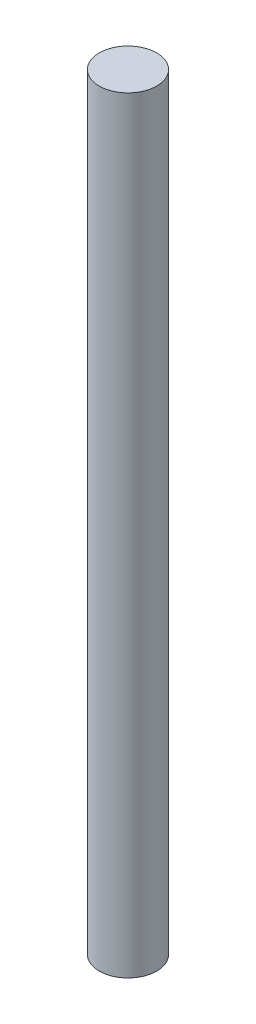
SolidWorks part; units mm, degrees
ref_plane "Ön Düzlem" through (0, 0, 0) normal (0, 0, 1) x (1, 0, 0)
ref_plane "Üst Düzlem" through (0, 0, 0) normal (0, 1, 0) x (1, 0, 0)
ref_plane "Sağ Düzlem" through (0, 0, 0) normal (1, 0, 0) x (0, 0, -1)
sketch "Çizim1" plane through (0, 0, 0) normal (0, 1, 0) x (1, 0, 0)
  circle A0 centre (0, 0) radius 3
extrude "Yükseklik-Ekstrüzyon1" add sketch "Çizim1" along normal blind 80
